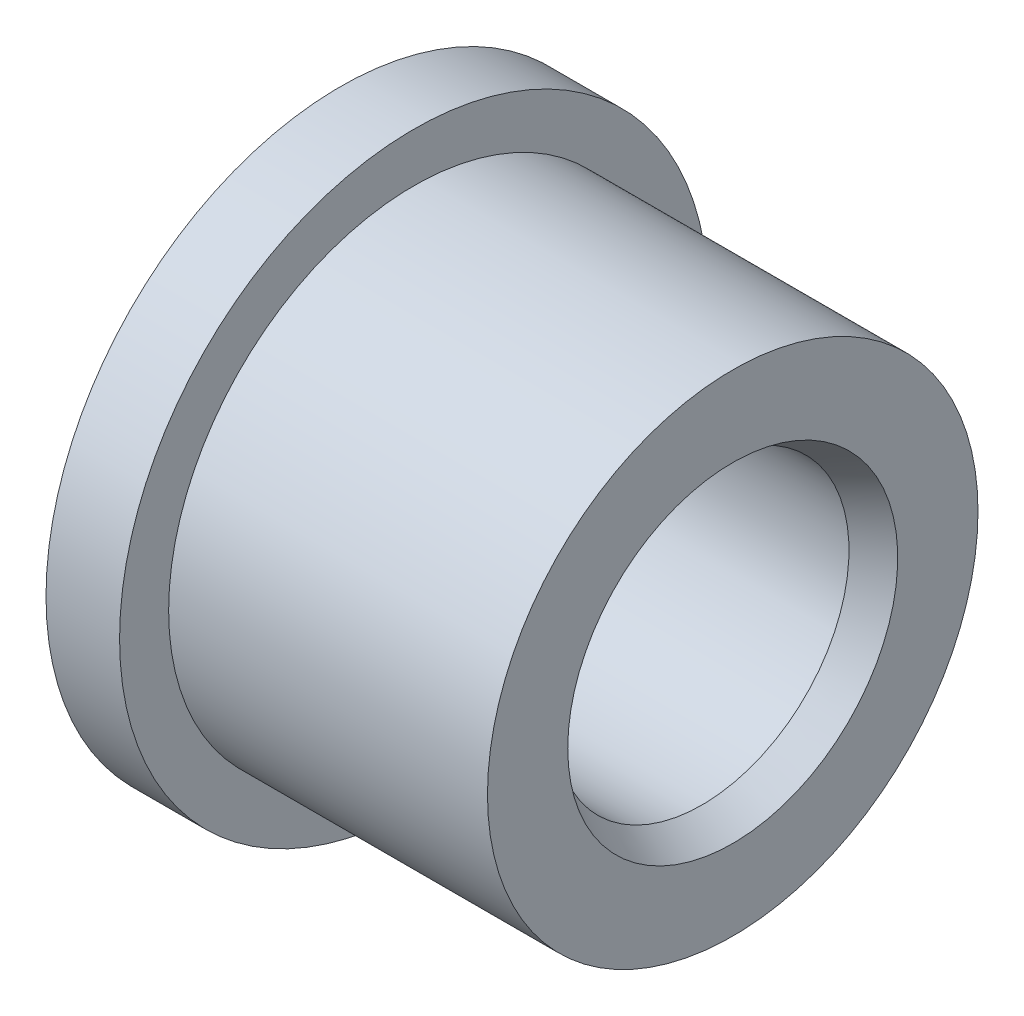
SolidWorks part; units mm, degrees
material "Nylon 101"
ref_plane "Front Plane" through (0, 0, 0) normal (0, 0, 1) x (1, 0, 0)
ref_plane "Top Plane" through (0, 0, 0) normal (0, 1, 0) x (1, 0, 0)
ref_plane "Right Plane" through (0, 0, 0) normal (1, 0, 0) x (0, 0, -1)
sketch "Sketch1" plane through (0, 0, 0) normal (0, 0, 1) x (1, 0, 0)
  line L0 (0, 2.3812) -> (0, 4.7625)
  line L1 (0, 4.7625) -> (1.1906, 4.7625)
  line L2 (1.1906, 4.7625) -> (1.1906, 3.9688)
  line L3 (1.1906, 3.9688) -> (6.35, 3.9688)
  line L4 (6.35, 3.9688) -> (6.35, 2.3812)
  line L5 (6.35, 2.3812) -> (0, 2.3812)
  line L6 (0, 0) -> (22.026, 0) construction
  dimension "D1" = 4.7625
  dimension "D2" = 7.9375
  dimension "D3" = 9.525
  dimension "D4" = 1.1906
  dimension "D5" = 6.35
revolve "Revolve1" add sketch "Sketch1" angle 360 about L6
chamfer "Chamfer1" distance 0.5 angle 30 2 edges at (6.35, 0, 2.3812) (0, 0, 2.3812)
